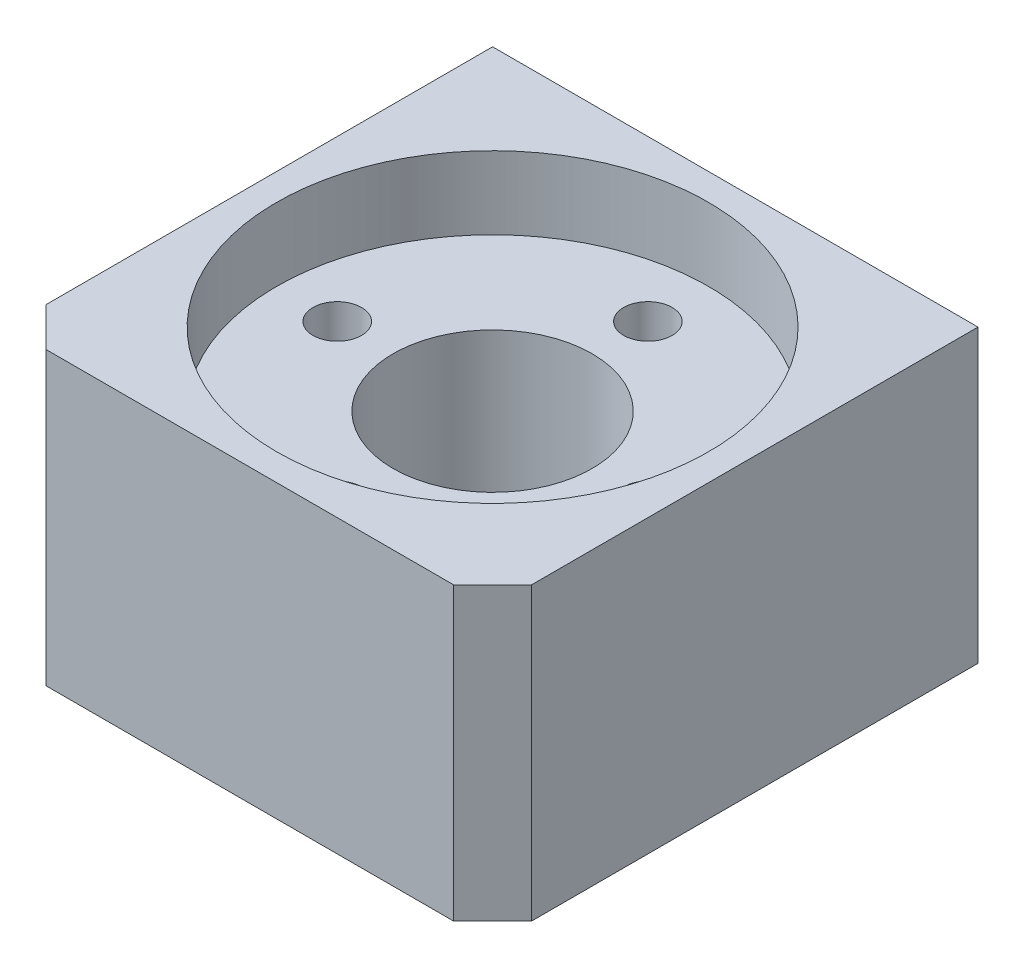
SolidWorks part; units mm, degrees
material "6061-T6 (SS)"
ref_plane "Front Plane" through (0, 0, 0) normal (0, 0, 1) x (1, 0, 0)
ref_plane "Top Plane" through (0, 0, 0) normal (0, 1, 0) x (1, 0, 0)
ref_plane "Right Plane" through (0, 0, 0) normal (1, 0, 0) x (0, 0, -1)
sketch "Sketch1" plane through (0, 0, 0) normal (0, 1, 0) x (1, 0, 0)
  line L1 (-12.5, 12.5) -> (12.5, 12.5)
  line L2 (-12.5, 12.5) -> (-12.5, -12.5)
  line L3 (-12.5, -12.5) -> (12.5, -12.5)
  line L4 (12.5, 12.5) -> (12.5, -12.5)
  line L5 (-12.5, 12.5) -> (12.5, -12.5) construction
  line L6 (-12.5, -12.5) -> (12.5, 12.5) construction
  point P0 (0, 0)
  dimension "D1" = 25
  dimension "D2" = 25
extrude "Boss-Extrude1" add sketch "Sketch1" along normal blind 15
sketch "Sketch2" plane through (0, 15, 0) normal (0, 1, 0) x (1, 0, 0)
  circle A0 centre (0, 0) radius 11.125
  dimension "D1" = 22.25
extrude "Cut-Extrude1" cut sketch "Sketch2" against normal blind 3.75
sketch "Sketch3" plane through (0, 11.25, 0) normal (0, 1, 0) x (1, 0, 0)
  circle A0 centre (0, 0) radius 5.125
  dimension "D1" = 10.25
extrude "Cut-Extrude2" cut sketch "Sketch3" against normal through all
sketch "Sketch4" plane through (0, 11.25, 0) normal (0, 1, 0) x (1, 0, 0)
  line L0 (0, 0) -> (0, 8) construction
  circle A0 centre (0, 0) radius 8 construction
  point P4 (8, 0)
  point P5 (0, 8)
  point P6 (0, -8)
  point P7 (-8, 0)
  dimension "D1" = 16
hole_wizard "M3x0.5 Tapped Hole1" positions "Sketch4" profile "Sketch5" tap size "M3x0.5" standard "ANSI Metric"
sketch "Sketch5" plane through (-8, 11.25, 0) normal (1, 0, 0) x (0, 0, 1)
  line L0 (0, 0) -> (0, 6.7511)
  line L1 (0, 6.7511) -> (1.25, 6)
  line L2 (1.25, 6) -> (1.25, 0)
  line L5 (1.25, 0) -> (0, 0)
  line L10 (0, 6.7511) -> (-1.25, 6) construction
  line L11 (0, -6.35) -> (0, 107.95) construction
  dimension "Tap Drill Dia." = 2.5
  dimension "Tap Drill Depth" = 6
  dimension "Drill Angle" = 118
cosmetic thread "Hole Thread1" parameters "D1"=6, "D2"=3
cosmetic thread "Hole Thread2" parameters "D1"=6, "D2"=3
cosmetic thread "Hole Thread3" parameters "D1"=6, "D2"=3
cosmetic thread "Hole Thread4" parameters "D1"=6, "D2"=3
sketch "Sketch6" plane through (0, 0, -12.5) normal (0, 0, -1) x (-1, 0, 0)
  line L0 (12.5, 7.5) -> (-12.5, 7.5) construction
  line L1 (12.5, 15) -> (12.5, 0) construction
  line L2 (-12.5, 15) -> (-12.5, 0) construction
  line L3 (0, 0) -> (0, 15) construction
  line L4 (-12.5, 15) -> (12.5, 15) construction
  point P11 (7.5, 7.5)
  point P12 (-7.5, 7.5)
  dimension "D1" = 15
hole_wizard "M4x0.7 Tapped Hole1" positions "Sketch6" profile "Sketch7" tap size "M4x0.7" standard "ANSI Metric"
sketch "Sketch7" plane through (7.5, 7.5, -12.5) normal (1, 0, 0) x (0, 1, 0)
  line L0 (0, 0) -> (0, 8.9914)
  line L1 (0, 8.9914) -> (1.65, 8)
  line L2 (1.65, 8) -> (1.65, 0)
  line L5 (1.65, 0) -> (0, 0)
  line L10 (0, 8.9914) -> (-1.65, 8) construction
  line L11 (0, -6.35) -> (0, 107.95) construction
  dimension "Tap Drill Dia." = 3.3
  dimension "Tap Drill Depth" = 8
  dimension "Drill Angle" = 118
cosmetic thread "Hole Thread5" parameters "D1"=8, "D2"=4
cosmetic thread "Hole Thread6" parameters "D1"=8, "D2"=4
chamfer "Chamfer1" distance 2 angle 45 2 edges at (-12.5, 7.5, 12.5) (12.5, 7.5, 12.5)
